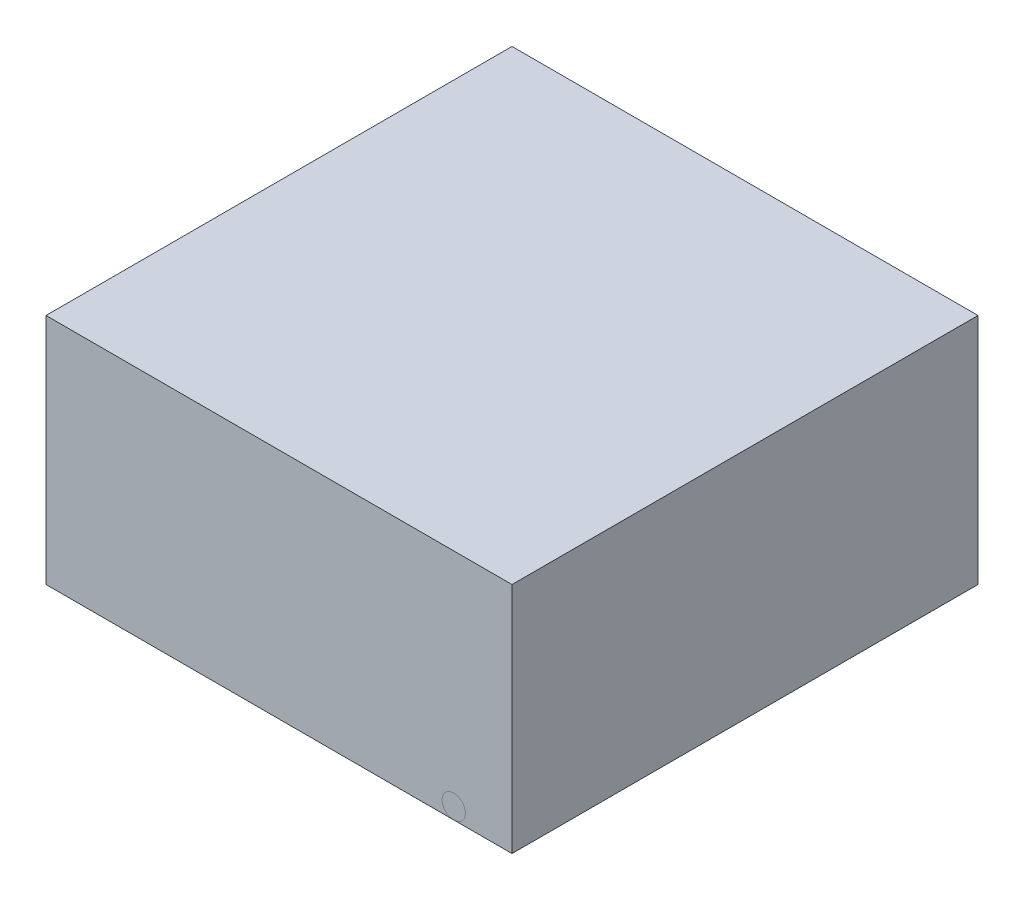
SolidWorks part; units mm, degrees
ref_plane "Front Plane" through (0, 0, 0) normal (0, 0, 1) x (1, 0, 0)
ref_plane "Top Plane" through (0, 0, 0) normal (0, 1, 0) x (1, 0, 0)
ref_plane "Right Plane" through (0, 0, 0) normal (1, 0, 0) x (0, 0, -1)
sketch "Sketch1" plane through (0, 0, 0) normal (0, 0, 1) x (1, 0, 0)
  line L1 (-10, -5) -> (10, -5)
  line L2 (-10, -5) -> (-10, 5)
  line L3 (-10, 5) -> (10, 5)
  line L4 (10, -5) -> (10, 5)
  line L5 (0, 5) -> (0, -5) construction
  line L6 (-10, 0) -> (10, 0) construction
  point P0 (0, 0)
  dimension "D1" = 20
  dimension "D2" = 10
extrude "Boss-Extrude1" add sketch "Sketch1" along normal blind 20
sketch "Sketch2" plane through (0, 0, 20) normal (0, 0, 1) x (1, 0, 0)
  line L0 (-10, -5) -> (10, -5) construction
  line L1 (0, 0) -> (0, -5) construction
  circle A0 centre (-7.5, -4.5) radius 0.5
  circle A1 centre (7.5, -4.5) radius 0.5
  dimension "D1" = 1
  dimension "D2" = 7.5
ref_plane "Plane1" through (7.5, 0, 0) normal (1, 0, 0) x (0, 0, -1)
sketch "Sketch3" plane through (7.5, 0, 0) normal (1, 0, 0) x (0, 0, -1)
  line L3 (-20, -4.5) -> (-5, -4.5)
  line L4 (-20, -4) -> (-20, -5) construction
  line L5 (-4, -3.5) -> (-4, 5)
  line L6 (-20, 5) -> (0, 5) construction
  arc A0 (-5, -4.5) -> (-4, -3.5) centre (-5, -3.5) ccw
  dimension "D1" = 1
  dimension "D2" = 15
sweep "ag/agcl electrodes" add profiles "Sketch2" path "Sketch3"
sketch "Sketch4" plane through (0, -5, 0) normal (0, 1, 0) x (1, 0, 0)
  line L0 (0, -11.4373) -> (0, -13.4201) construction
  line L1 (-2.0803, -12.5) -> (1.6023, -12.5) construction
  spline S0 degree 3 poles (-2.0861, -12.5392) (-1.3776, -12.1296) (-0.8241, -11.549) (0.2513, -11.3226) (1.3726, -11.7466) (2.6529, -13.5718) (0.7805, -13.1045) (-0.1221, -13.5063) (-0.9948, -13.461) (-1.5864, -13.1169) (-2.0861, -12.5392) (-1.3776, -12.1296) (-0.8241, -11.549) knots -0.204834 -0.133435 -0.089031 0 0.049563 0.182818 0.303261 0.461561 0.613381 0.684438 0.795166 0.866565 0.910969 1 1.049563 1.182818 1.303261 only from (-1.3298, -12.0471) to (-1.3298, -12.0471)
extrude "slice" add sketch "Sketch4" along normal blind 0.3 separate body
